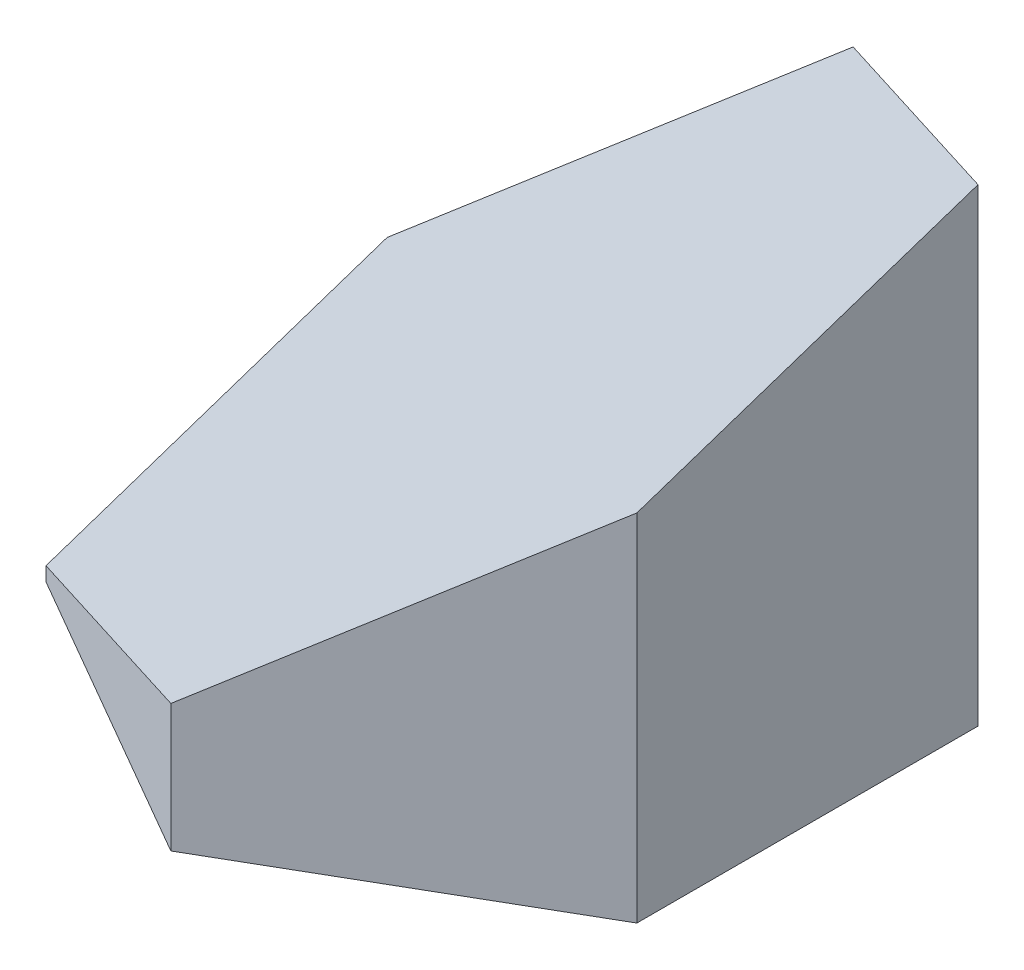
SolidWorks part; units mm, degrees
ref_plane "VP" through (0, 0, 0) normal (0, 0, 1) x (1, 0, 0)
ref_plane "HP" through (0, 0, 0) normal (0, 1, 0) x (1, 0, 0)
ref_plane "Right Plane" through (0, 0, 0) normal (1, 0, 0) x (0, 0, -1)
sketch "Sketch1" plane through (0, 0, 0) normal (0, 1, 0) x (1, 0, 0)
  line L1 (114.282, -73) -> (114.282, -33)
  line L2 (114.282, -33) -> (79.641, -13)
  line L3 (79.641, -13) -> (45, -33)
  line L4 (45, -33) -> (45, -73)
  line L5 (45, -73) -> (79.641, -93)
  line L6 (79.641, -93) -> (114.282, -73)
  circle A0 centre (79.641, -53) radius 34.641 construction
  dimension "D1" = 13
  dimension "D2" = 45
  dimension "D3" = 40
extrude "Boss-Extrude1" add sketch "Sketch1" along normal blind 90
sketch "Sketch2" plane through (0, 0, 0) normal (0, 1, 0) x (1, 0, 0)
  point P0 (0, 0)
sketch "Sketch3" plane through (0, 0, 0) normal (0, 1, 0) x (1, 0, 0)
  line L0 (0, 0) -> (32.8726, -56.937) construction
  line L1 (0, 0) -> (94.0809, 0) construction
  dimension "D1" = 60
sketch "Sketch4" plane through (0, 0, 0) normal (0, 0, 1) x (1, 0, 0)
  line L0 (0, 0) -> (93.1206, 53.7632) construction
  line L1 (0, 0) -> (32.8726, 0) construction
  dimension "D1" = 30
ref_plane "VTH" through (0, 0, 0) normal (0.4804, -0.8321, -0.2774) x (-0.8771, -0.4557, -0.1519)
other "SurfaceCut1"
